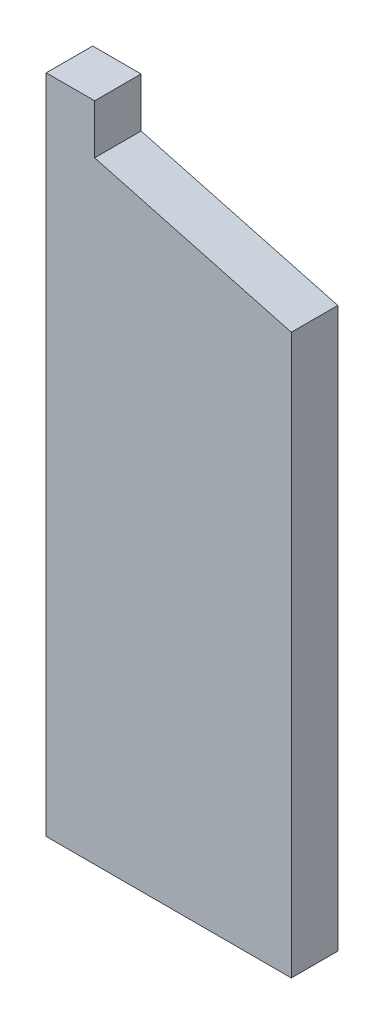
SolidWorks part; units mm, degrees
ref_plane "前视基准面" through (0, 0, 0) normal (0, 0, 1) x (1, 0, 0)
ref_plane "上视基准面" through (0, 0, 0) normal (0, 1, 0) x (1, 0, 0)
ref_plane "右视基准面" through (0, 0, 0) normal (1, 0, 0) x (0, 0, -1)
sketch "草图1" plane through (0, 0, 0) normal (0, 0, 1) x (1, 0, 0)
  line L1 (0, 0) -> (49.6, 0)
  line L2 (0, 0) -> (0, -133.83)
  line L3 (0, -133.83) -> (49.6, -133.83)
  line L4 (49.6, 0) -> (49.6, -133.83)
  line L5 (9.8, 0) -> (39.8, 0)
  line L6 (9.8, 0) -> (9.8, -10)
  line L7 (9.8, -10) -> (39.8, -10)
  line L8 (39.8, 0) -> (39.8, -10)
  point P9 (24.8, 0)
  dimension "D1" = 10
  dimension "D2" = 49.6
  dimension "D3" = 30
  dimension "D4" = 123.83
extrude "凸台-拉伸1" add sketch "草图1" along normal blind 9.4 contours L1 L8 L7 L6 L2 L3 L4
draft "拔模5" [suppressed] type of draft neutral plane draft angle 15 faces to draft 1 parameters "D1"=15
sketch "草图2" plane through (0, 0, 9.4) normal (0, 0, 1) x (1, 0, 0)
  line L0 (9.8, -10) -> (49.6, -20.6644)
  line L1 (49.6, 0) -> (49.6, -133.83) construction
  line L2 (9.8, -10) -> (39.8, -10) construction
  dimension "D1" = 15
extrude "切除-拉伸1" cut sketch "草图2" against normal through all and the other way through all
